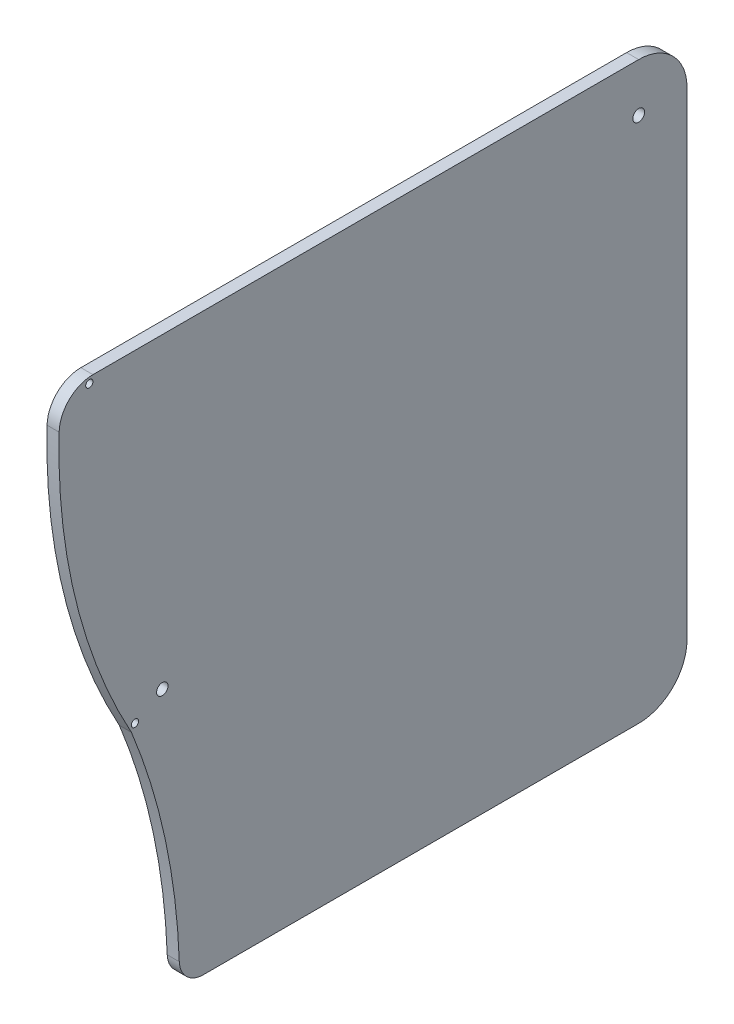
SolidWorks part; units mm, degrees
ref_plane "Front Plane" through (0, 0, 0) normal (0, 0, 1) x (1, 0, 0)
ref_plane "Top Plane" through (0, 0, 0) normal (0, 1, 0) x (1, 0, 0)
ref_plane "Right Plane" through (0, 0, 0) normal (1, 0, 0) x (0, 0, -1)
sketch "Sketch1" plane through (0, 0, 0) normal (1, 0, 0) x (0, 0, -1)
  line L1 (-82.55, 75.565) -> (82.55, 75.565)
  line L2 (-82.55, 75.565) -> (-82.55, -75.565)
  line L3 (-82.55, -75.565) -> (82.55, -75.565)
  line L4 (82.55, 75.565) -> (82.55, -75.565)
  line L9 (69.85, 75.565) -> (69.85, -75.565) construction
  circle A0 centre (69.85, 62.865) radius 1.55
  arc A1 (69.85, -75.565) -> (82.55, -62.865) centre (69.85, -62.865) ccw
  arc A2 (82.55, 62.865) -> (69.85, 75.565) centre (69.85, 62.865) ccw
  point P4 (-82.55, 0)
  point P6 (0, 75.565)
  dimension "D6" = 3.1
  dimension "D1" = 165.1
  dimension "D3" = 151.13
  dimension "D4" = 12.7
  dimension "D5" = 12.7
  dimension "D7" = 12.7
extrude "Boss-Extrude1" add sketch "Sketch1" along normal blind 3.175 contours L9 L1 L2 L3 A0 | L1 L9 A1 L4
sketch "Sketch2" plane through (3.175, 0, 0) normal (1, 0, 0) x (0, 0, -1)
  line L0 (-63.5, -75.565) -> (-50.8, -75.565)
  line L2 (-82.55, 62.865) -> (-82.55, -75.565)
  line L3 (-82.55, -75.565) -> (-63.5, -75.565)
  line L5 (-82.55, 75.565) -> (-82.0199, 75.565)
  line L6 (-82.55, 75.565) -> (69.85, 75.565) construction
  line L7 (-82.55, 75.565) -> (-82.55, 62.865)
  line L8 (-63.5, -10.9153) -> (-63.5, -75.565)
  line L9 (82.55, 62.865) -> (82.55, -62.865) construction
  line L11 (-50.8, 75.565) -> (-50.8, -75.565) construction
  line L12 (-82.55, -75.565) -> (69.85, -75.565) construction
  arc A1 (-82.0199, 75.565) -> (-63.5, -10.9153) centre (69.85, 62.865) ccw
  arc A4 (-50.8, -75.565) -> (-63.5, -10.9153) centre (-221.7004, -75.565) ccw
  line M6 (69.85, 75.565) -> (-82.55, 75.565)
  line M7 (-82.55, 75.565) -> (-82.55, -75.565)
  line M8 (-82.55, -75.565) -> (69.85, -75.565)
  dimension "D1" = 146.05
  dimension "D2" = 133.35
extrude "Cut-Extrude1" cut sketch "Sketch2" against normal through all contours A1 M7 M8 | A1 M6 M7 | A4 L8 M8
fillet "Fillet1" radius 8.89 1 edges at (1.5875, 75.565, 82.0199)
sketch "Sketch3" plane through (3.175, 0, 0) normal (1, 0, 0) x (0, 0, -1)
  circle A0 centre (-55.3788, -5.135) radius 1.5
  circle A1 centre (69.85, 62.865) radius 1.55 construction
  dimension "D1" = 3
  dimension "D2" = 142.5
  dimension "D3" = 68
extrude "Cut-Extrude2" cut sketch "Sketch3" against normal through all
sketch "Sketch4" plane through (3.175, 0, 0) normal (1, 0, 0) x (0, 0, -1)
  line L0 (-73.6094, 72.39) -> (-73.6094, 75.565)
  line L1 (-60.7219, -9.3782) -> (-63.5, -10.9153)
  line L2 (-74.5619, 73.9775) -> (-73.6094, 73.9775) construction
  line L3 (-62.1109, -10.1468) -> (-62.5721, -9.3134) construction
  arc A0 (-82.4963, 66.911) -> (-63.5, -10.9153) centre (69.85, 62.865) ccw construction
  arc A1 (-73.6094, 75.565) -> (-82.4963, 66.911) centre (-73.6094, 66.675) ccw construction
  arc A2 (-82.4963, 66.911) -> (-63.5, -10.9153) centre (69.85, 62.865) ccw
  arc A3 (-73.6094, 75.565) -> (-82.4963, 66.911) centre (-73.6094, 66.675) ccw
  arc A4 (-73.6094, 72.39) -> (-79.3224, 66.8267) centre (-73.6094, 66.675) ccw
  arc A5 (-79.3224, 66.8267) -> (-60.7219, -9.3782) centre (69.85, 62.865) ccw
  circle A6 centre (-74.5619, 73.9775) radius 0.9525
  circle A7 centre (-62.5721, -9.3134) radius 0.9525
  dimension "D2" = 1.905
  dimension "D1" = 3.175
extrude "Cut-Extrude3" cut sketch "Sketch4" against normal through all contours A6 | A7
fillet "Fillet2" radius 6.35 1 edges at (1.5875, -75.565, 50.8)
equation "\"bottomThickness\"= .25in"
equation "\"wallThickness\"= .125in"
equation "\"D1@Boss-Extrude1\"=\"wallThickness\""
